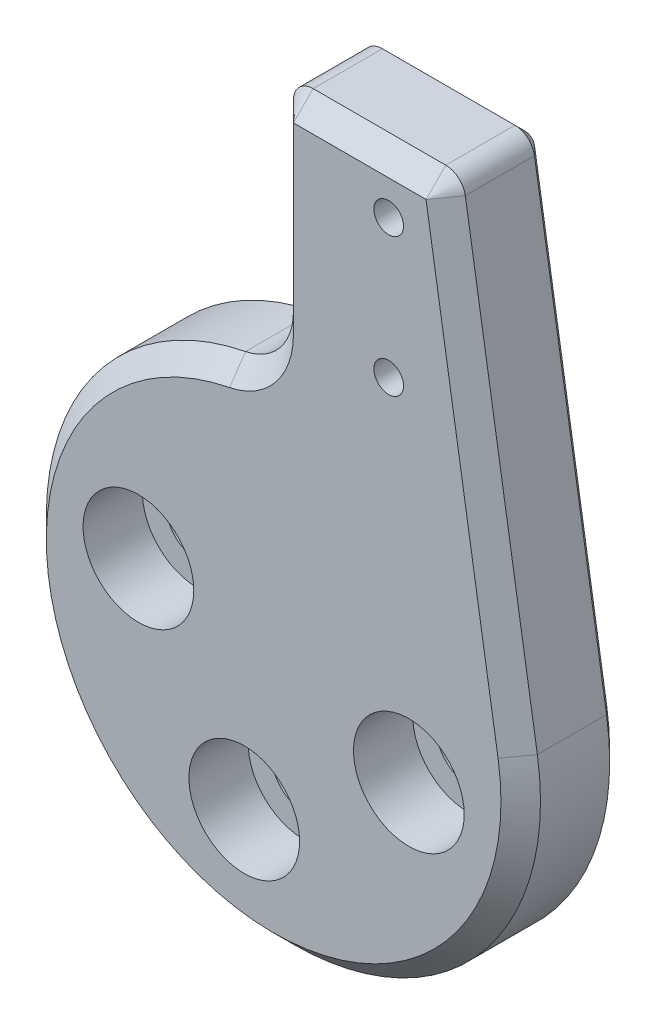
SolidWorks part; units mm, degrees
ref_plane "Front Plane" through (0, 0, 0) normal (0, 0, 1) x (1, 0, 0)
ref_plane "Top Plane" through (0, 0, 0) normal (0, 1, 0) x (1, 0, 0)
ref_plane "Right Plane" through (0, 0, 0) normal (1, 0, 0) x (0, 0, -1)
sketch "Sketch1" plane through (0, 0, 0) normal (0, 0, 1) x (1, 0, 0)
  line L0 (0, 0) -> (0, 11.5555) construction
  line L1 (0.5606, 13) -> (0.01, 13)
  line L2 (0.5606, 13) -> (0.5606, 25.4916) construction
  line L3 (0.5606, 13) -> (6.8007, 13) construction
  line L4 (6.8007, 13) -> (6.8007, 25.4916) construction
  line L5 (0.5606, 25.4916) -> (6.8007, 25.4916) construction
  line L6 (-3.2532, 27.1421) -> (0.01, 13) construction
  line L7 (1, 25.4916) -> (7.7086, 25.4916)
  line L8 (8.6959, 24.6504) -> (12.3414, 1.985)
  line L9 (0.5606, 25.4916) -> (0, 25.4916)
  line L10 (0, 24.4916) -> (0, 15.2069)
  line L11 (0, 12.5) -> (0, 30.616) construction
  arc A0 (-2.4194, 12.2636) -> (12.3414, 1.985) centre (0, 0) ccw
  circle A1 centre (-6.8401, 1.4875) radius 1.6
  circle A2 centre (-1.4875, -6.8401) radius 1.6
  circle A3 centre (6.8401, -1.4875) radius 1.6
  circle A4 centre (5.8209, 15.75) radius 0.75
  circle A5 centre (5.8209, 22.75) radius 0.75
  arc A6 (0, 24.4916) -> (1, 25.4916) centre (1, 24.4916) cw
  arc A7 (7.7086, 25.4916) -> (8.6959, 24.6504) centre (7.7086, 24.4916) cw
  arc A8 (-2.4194, 12.2636) -> (0, 15.2069) centre (-3, 15.2069) ccw
  dimension "D3" = 1.5
  dimension "D5" = 1
  dimension "D6" = 3
  dimension "D7" = 3.2
  dimension "D1" = 13
  dimension "D2" = 2.75
  dimension "D4" = 7
extrude "Boss-Extrude1" add sketch "Sketch1" along normal blind 5
chamfer "Chamfer1" distance 1 angle 45 7 edges at (-0.6825, 13.3019, 5) (-7.1431, -10.258, 5) (0, 19.8493, 5) (10.5187, 13.3177, 5) (0.2929, 25.1987, 5) (8.3571, 25.2528, 5) (4.3543, 25.4916, 5)
sketch "Sketch2" plane through (0, 0, 5) normal (0, 0, 1) x (1, 0, 0)
  circle A0 centre (-6.8401, 1.4875) radius 2.8
  circle A1 centre (-1.4875, -6.8401) radius 2.8
  circle A2 centre (6.8401, -1.4875) radius 2.8
  dimension "D1" = 5.6
extrude "Cut-Extrude1" cut sketch "Sketch2" against normal blind 3
chamfer "Chamfer3" distance 0.5 angle 45 7 edges at (-0.6825, 13.3019, 0) (-7.1431, -10.258, 0) (0, 19.8493, 0) (10.5187, 13.3177, 0) (0.2929, 25.1987, 0) (8.3571, 25.2528, 0) (4.3543, 25.4916, 0)
